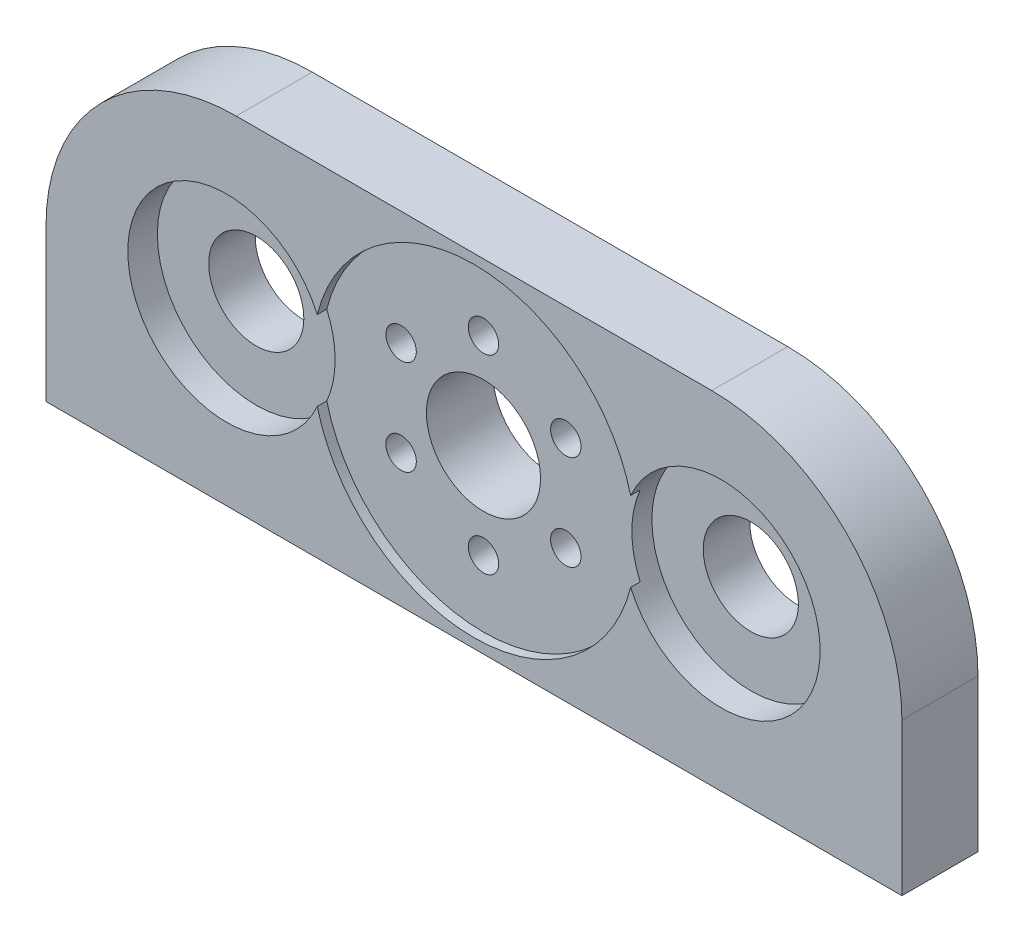
SolidWorks part; units mm, degrees
ref_plane "Front Plane" through (0, 0, 0) normal (0, 0, 1) x (1, 0, 0)
ref_plane "Top Plane" through (0, 0, 0) normal (0, 1, 0) x (1, 0, 0)
ref_plane "Right Plane" through (0, 0, 0) normal (1, 0, 0) x (0, 0, -1)
sketch "Sketch1" plane through (0, 0, 0) normal (0, 1, 0) x (1, 0, 0)
  line L1 (0, 0) -> (-45, 0)
  line L2 (0, 0) -> (0, 4)
  line L3 (0, 4) -> (-45, 4)
  line L4 (-45, 0) -> (-45, 4)
  dimension "D1" = 45
  dimension "D2" = 4
extrude "Boss-Extrude1" add sketch "Sketch1" along normal blind 18
sketch "Sketch2" plane through (0, 0, 0) normal (0, 0, 1) x (1, 0, 0)
  line L0 (-22.5, 18) -> (-22.5, 0) construction
  line L1 (-45, 18) -> (0, 18) construction
  line L2 (-45, 0) -> (0, 0) construction
  circle A0 centre (-22.5, 9) radius 8.5
  dimension "D1" = 17
extrude "Cut-Extrude2" cut sketch "Sketch2" against normal blind 0.5
sketch "Sketch3" plane through (0, 0, -0.5) normal (0, 0, 1) x (1, 0, 0)
  line L0 (-22.5, 17.5) -> (-22.5, 0.5) construction
  circle A0 centre (-22.5, 9) radius 8.5 construction
  circle A1 centre (-22.5, 9) radius 8.5 construction
  circle A2 centre (-22.5, 9) radius 3
  dimension "D1" = 6
extrude "Cut-Extrude3" cut sketch "Sketch3" against normal through all
sketch "Sketch4" plane through (0, 0, 0) normal (0, 0, 1) x (1, 0, 0)
  line L0 (-22.5, 18) -> (-22.5, 0) construction
  line L1 (-45, 18) -> (0, 18) construction
  line L2 (-45, 0) -> (0, 0) construction
  circle A0 centre (-35.5, 9) radius 2.5
  circle A1 centre (-9.5, 9) radius 2.5
  dimension "D1" = 5
  dimension "D2" = 13
  dimension "D3" = 9
extrude "Cut-Extrude4" cut sketch "Sketch4" against normal through all contours A0 | A1
sketch "Sketch6" plane through (0, 0, -0.5) normal (0, 0, 1) x (1, 0, 0)
  circle A0 centre (-22.5, 9) radius 5
  circle A1 centre (-22.5, 14) radius 0.8
  circle A2 centre (-18.1699, 11.5) radius 0.8
  circle A3 centre (-18.1699, 6.5) radius 0.8
  circle A4 centre (-22.5, 4) radius 0.8
  circle A5 centre (-26.8301, 6.5) radius 0.8
  circle A6 centre (-26.8301, 11.5) radius 0.8
  point P17 (-22.5, 9)
  dimension "D1" = 10
  dimension "D2" = 1.6
  dimension "D3" = 6
extrude "Cut-Extrude6" cut sketch "Sketch6" against normal through all contours A6 | A1 | A2 | A3 | A4 | A5
fillet "Fillet1" radius 10 2 edges at (0, 18, -2) (-45, 18, -2)
sketch "Sketch7" plane through (0, 0, 0) normal (0, 0, 1) x (1, 0, 0)
  line L0 (-35.5, 11.5) -> (-35.5, 6.5) construction
  line L1 (-22.5, 18) -> (-22.5, 0) construction
  line L2 (-35, 18) -> (-10, 18) construction
  line L3 (-45, 0) -> (0, 0) construction
  circle A0 centre (-35.5, 9) radius 2.5 construction
  circle A1 centre (-35.5, 9) radius 5.2
  circle A2 centre (-9.5, 9) radius 5.2
  dimension "D1" = 10.4
extrude "Cut-Extrude7" cut sketch "Sketch7" against normal blind 1.555
